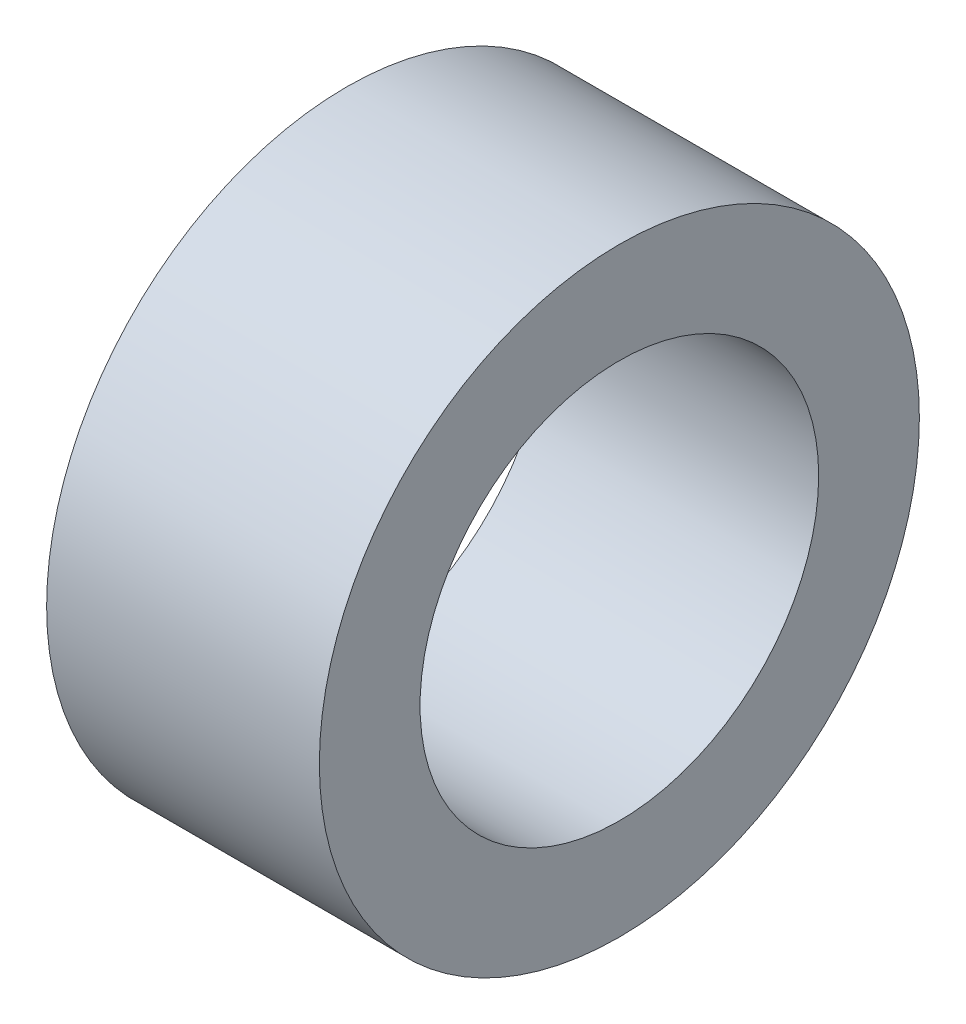
SolidWorks part; units mm, degrees
ref_plane "Plan de face" through (0, 0, 0) normal (0, 0, 1) x (1, 0, 0)
ref_plane "Plan de dessus" through (0, 0, 0) normal (0, 1, 0) x (1, 0, 0)
ref_plane "Plan de droite" through (0, 0, 0) normal (1, 0, 0) x (0, 0, -1)
sketch "Esquisse1" plane through (0, 0, 0) normal (0, 0, 1) x (1, 0, 0)
  line L0 (-11.3414, 0) -> (22.0061, 0) construction
  line L1 (0, 0) -> (13, 0)
  line L2 (0, 0) -> (0, 14.3)
  line L3 (0, 14.3) -> (13, 14.3)
  line L4 (13, 0) -> (13, 14.3)
  dimension "D1" = 14.3
  dimension "D2" = 13
revolve "Révolution1" add sketch "Esquisse1" angle 360 about L0
sketch "Esquisse2" plane through (13, 0, 0) normal (1, 0, 0) x (0, 0, -1)
  circle A0 centre (0, 0) radius 9.5
  dimension "D1" = 19
extrude "Enlèv. mat.-Extru.1" cut sketch "Esquisse2" against normal through all
